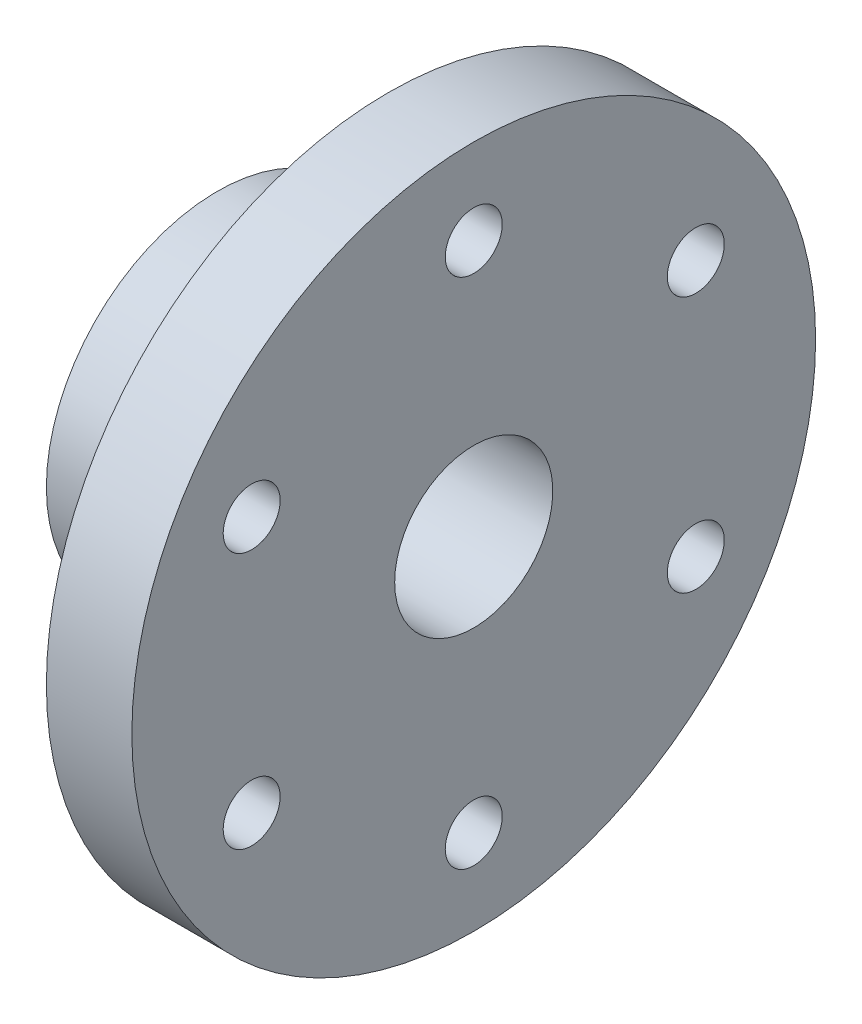
SolidWorks part; units mm, degrees
ref_plane "Front Plane" through (0, 0, 0) normal (0, 0, 1) x (1, 0, 0)
ref_plane "Top Plane" through (0, 0, 0) normal (0, 1, 0) x (1, 0, 0)
ref_plane "Right Plane" through (0, 0, 0) normal (1, 0, 0) x (0, 0, -1)
sketch "Sketch1" plane through (0, 0, 0) normal (0, 0, 1) x (1, 0, 0)
  line L0 (-11.6129, 0) -> (15.7189, 0) construction
  line L1 (-25.7005, 11.1) -> (-25.7005, 24)
  line L2 (-25.7005, 24) -> (-1.7005, 24)
  line L3 (-1.7005, 24) -> (-1.7005, 48)
  line L4 (-1.7005, 48) -> (10.2995, 48)
  line L5 (10.2995, 48) -> (10.2995, 11.1)
  line L6 (10.2995, 11.1) -> (-25.7005, 11.1)
  dimension "D1" = 48
  dimension "D2" = 12
  dimension "D3" = 24
  dimension "D4" = 24
  dimension "D5" = 11.1
revolve "Revolve1" add sketch "Sketch1" angle 360 about L0
sketch "Sketch2" plane through (-1.7005, 0, 0) normal (-1, 0, 0) x (0, 0, 1)
  line L0 (0, -36) -> (0, 36) construction
  line L1 (-31.1769, 18) -> (31.1769, -18) construction
  line L2 (31.1769, 18) -> (-31.1769, -18) construction
  circle A0 centre (0, 0) radius 36 construction
  circle A9 centre (0, 36) radius 4
  circle A10 centre (31.1769, 18) radius 4
  circle A11 centre (31.1769, -18) radius 4
  circle A12 centre (0, -36) radius 4
  circle A13 centre (-31.1769, -18) radius 4
  circle A14 centre (-31.1769, 18) radius 4
  point P22 (0, 0)
  dimension "D1" = 72
  dimension "D4" = 8
  dimension "D5" = 6
extrude "Cut-Extrude1" cut sketch "Sketch2" against normal up to surface (12 mm away) up to face at (10.2995, 0, 48)
ref_plane "Plane1" through (0, 0, 24) normal (0, 0, 1) x (1, 0, 0)
sketch "Sketch3" plane through (0, 0, 24) normal (0, 0, 1) x (1, 0, 0)
  line L0 (-25.7005, 0) -> (-1.7005, 0) construction
  line L1 (-25.7005, 24) -> (-25.7005, -24) construction
  line L2 (-1.7005, 48) -> (-1.7005, -48) construction
  circle A0 centre (-13.7005, 0) radius 4
  dimension "D1" = 8
extrude "Cut-Extrude2" cut sketch "Sketch3" against normal up to surface (12.9 mm away) up to face at (10.2995, 0, 11.1)
sketch "Sketch4" plane through (-25.7005, 0, 0) normal (-1, 0, 0) x (0, 0, 1)
  circle A0 centre (0, 0) radius 8.5
